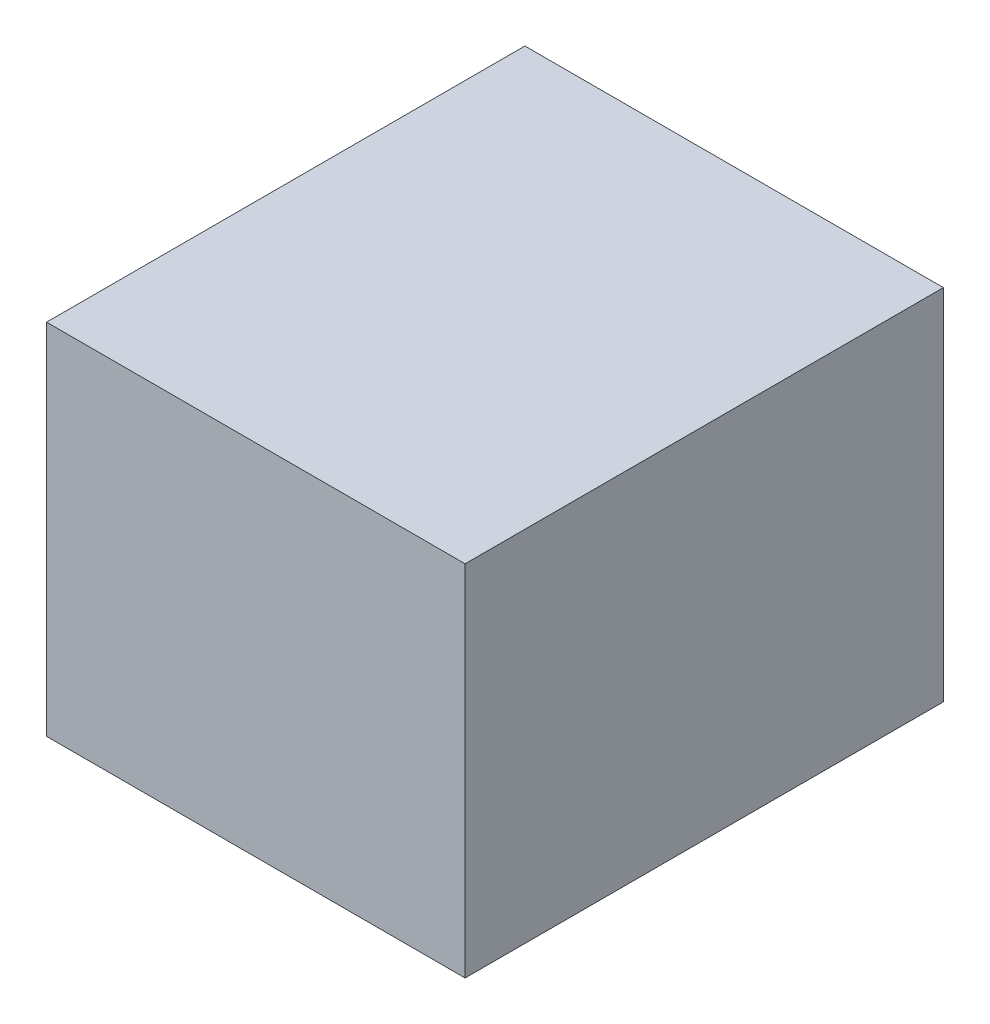
SolidWorks part; units mm, degrees
ref_plane "Front Plane" through (0, 0, 0) normal (0, 0, 1) x (1, 0, 0)
ref_plane "Top Plane" through (0, 0, 0) normal (0, 1, 0) x (1, 0, 0)
ref_plane "Right Plane" through (0, 0, 0) normal (1, 0, 0) x (0, 0, -1)
sketch "Sketch1" plane through (0, 0, 0) normal (0, 1, 0) x (1, 0, 0)
  line L0 (-355.6, 406.4) -> (355.6, -406.4) construction
  line L1 (-355.6, 406.4) -> (355.6, 406.4)
  line L2 (-355.6, 406.4) -> (-355.6, -406.4)
  line L3 (-355.6, -406.4) -> (355.6, -406.4)
  line L4 (355.6, 406.4) -> (355.6, -406.4)
  dimension "D1" = 711.2
  dimension "D2" = 812.8
extrude "Boss-Extrude1" add sketch "Sketch1" along normal mid plane 609.6
